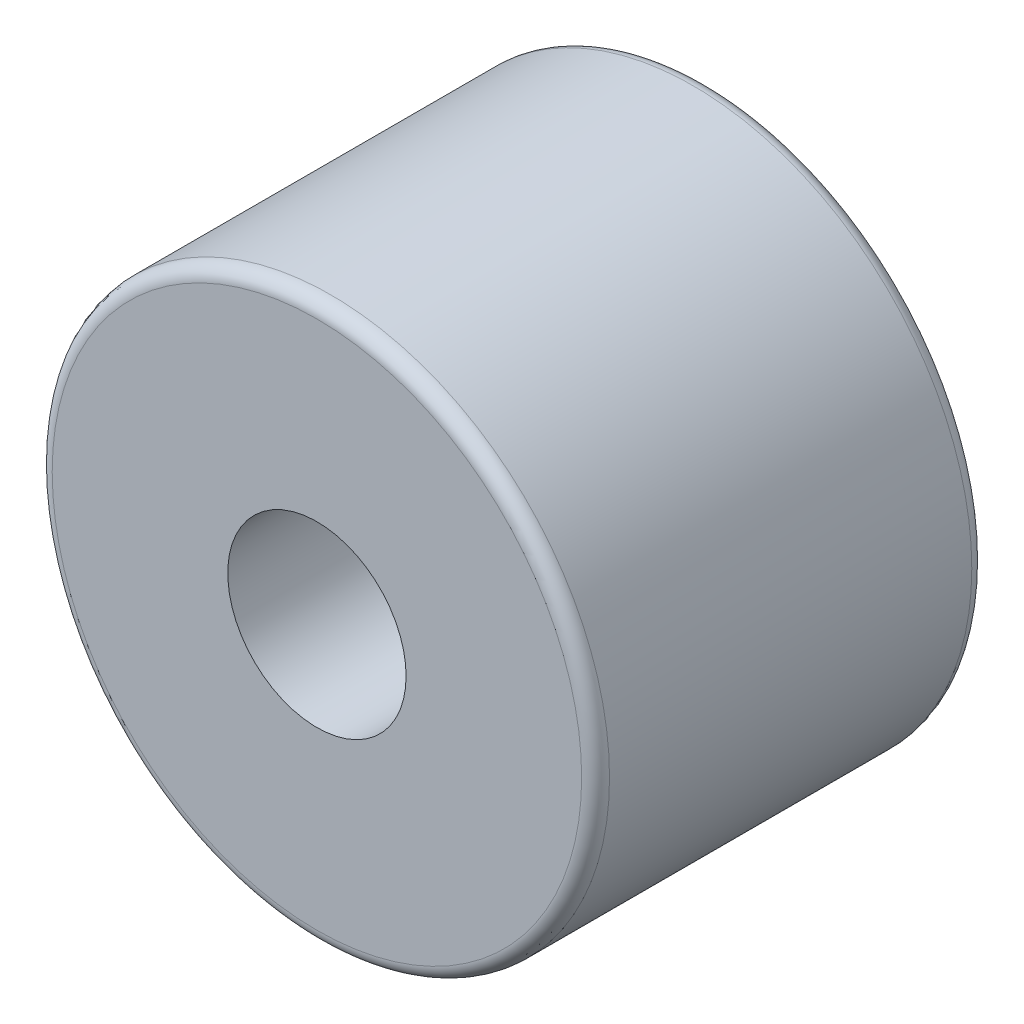
SolidWorks part; units mm, degrees
material "Plastique personnalisé"
ref_plane "Plan de face" through (0, 0, 0) normal (0, 0, 1) x (1, 0, 0)
ref_plane "Plan de dessus" through (0, 0, 0) normal (0, 1, 0) x (1, 0, 0)
ref_plane "Plan de droite" through (0, 0, 0) normal (1, 0, 0) x (0, 0, -1)
sketch "Esquisse1" plane through (0, 0, 0) normal (0, 0, 1) x (1, 0, 0)
  circle A0 centre (0, 0) radius 1.6
  circle A1 centre (0, 0) radius 5
extrude "Boss.-Extru.1" add sketch "Esquisse1" along normal blind 7
fillet "Congé1" radius 0.25 1 edges at (5, 0, 7)
fillet "Congé2" radius 0.25 1 edges at (5, 0, 0)
